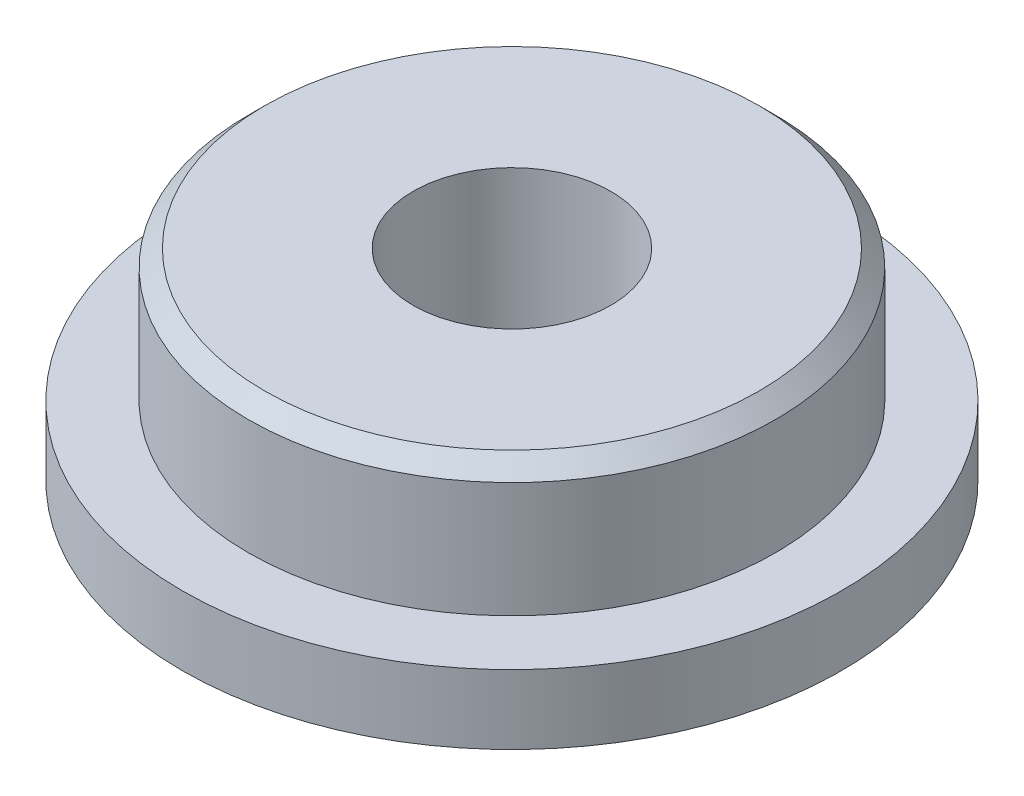
SolidWorks part; units mm, degrees
ref_plane "Front Plane" through (0, 0, 0) normal (0, 0, 1) x (1, 0, 0)
ref_plane "Top Plane" through (0, 0, 0) normal (0, 1, 0) x (1, 0, 0)
ref_plane "Right Plane" through (0, 0, 0) normal (1, 0, 0) x (0, 0, -1)
sketch "Sketch1" plane through (0, 0, 0) normal (0, 1, 0) x (1, 0, 0)
  circle A0 centre (0, 0) radius 5
  dimension "D1" = 10
extrude "Boss-Extrude1" add sketch "Sketch1" along normal blind 1.05
sketch "Sketch2" plane through (0, 1.05, 0) normal (0, 1, 0) x (1, 0, 0)
  circle A0 centre (0, 0) radius 4
  dimension "D1" = 8
extrude "Boss-Extrude2" add sketch "Sketch2" along normal blind 2
sketch "Sketch3" plane through (0, 3.05, 0) normal (0, 1, 0) x (1, 0, 0)
  circle A0 centre (0, 0) radius 1.5
extrude "Cut-Extrude1" cut sketch "Sketch3" against normal blind 12
chamfer "Chamfer2" distance 0.25 angle 45 1 edges at (0, 3.05, 4)
